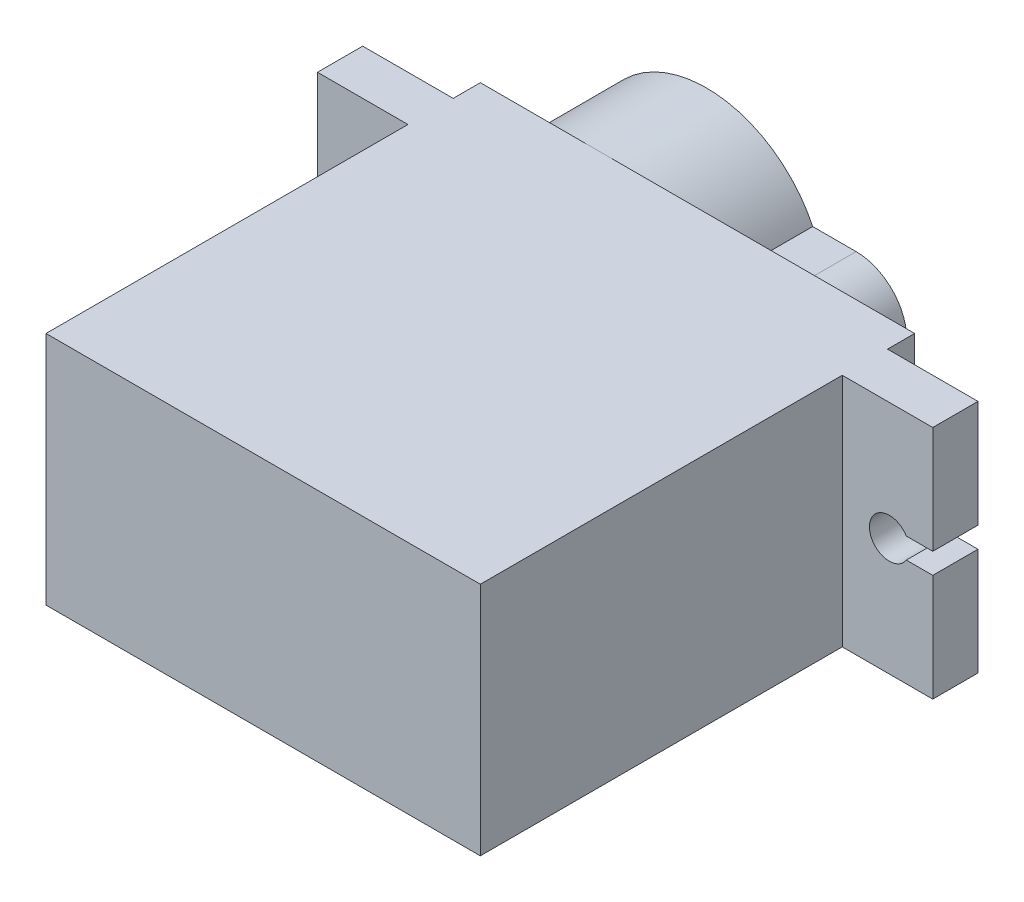
SolidWorks part; units mm, degrees
ref_plane "前视基准面" through (0, 0, 0) normal (0, 0, 1) x (1, 0, 0)
ref_plane "上视基准面" through (0, 0, 0) normal (0, 1, 0) x (1, 0, 0)
ref_plane "右视基准面" through (0, 0, 0) normal (1, 0, 0) x (0, 0, -1)
sketch "草图1" plane through (0, 0, 0) normal (0, 0, 1) x (1, 0, 0)
  line L0 (0, 0) -> (24, 0)
  line L5 (0, 0) -> (0, 13)
  line L6 (24, 0) -> (24, 13)
  line L7 (0, 13) -> (24, 13)
extrude "凸台-拉伸1" add sketch "草图1" along normal blind 24
ref_plane "基准面4" through (0, 0, 1.5) normal (0, 0, 1) x (1, 0, 0)
sketch "草图2" plane through (0, 0, 1.5) normal (0, 0, 1) x (1, 0, 0)
  line L0 (-5, 13) -> (29, 13)
  line L1 (-5, 13) -> (-5, 0)
  line L2 (29, 13) -> (29, 0)
  line L3 (-5, 0) -> (29, 0)
extrude "凸台-拉伸2" add sketch "草图2" along normal blind 2.5
ref_point "点2"
ref_point "点6"
ref_point "点7"
ref_point "点3"
sketch "草图6" plane through (0, 0, 1.5) normal (0, 0, 1) x (1, 0, 0)
  line L0 (-2.6, 6.5) -> (-2.6, 10)
  line L1 (-2.6, 6.5) -> (-2.6, 3)
  line L2 (-5, 7.0748) -> (-3.5379, 7.0748)
  line L3 (-5, 7.0748) -> (-5, 5.9252)
  line L4 (-5, 5.9252) -> (-3.5379, 5.9252)
  line L5 (12, 13) -> (12, 0) construction
  line L6 (29, 5.9252) -> (27.5379, 5.9252)
  line L7 (29, 7.0748) -> (29, 5.9252)
  line L8 (29, 7.0748) -> (27.5379, 7.0748)
  line L9 (26.6, 6.5) -> (26.6, 3)
  line L10 (26.6, 6.5) -> (26.6, 10)
  arc A0 (-3.5379, 5.9252) -> (-3.5379, 7.0748) centre (-2.6, 6.5) ccw
  arc A1 (27.5379, 5.9252) -> (27.5379, 7.0748) centre (26.6, 6.5) cw
ref_point "点4"
ref_point "点5"
hole_wizard "大小mm 暗销孔13" positions "草图24" profile "草图25" hole size "Ø1.0" standard "ISO"
sketch "草图24" plane through (0, 0, 1.5) normal (0, 0, -1) x (-1, 0, 0)
  point P0 (2.6, 10)
  point P3 (2.6, 3)
  point P6 (-26.6, 10)
  point P9 (-26.6, 3)
sketch "草图25" plane through (-2.6, 10, 1.5) normal (1, 0, 0) x (0, 1, 0)
  line L0 (0, 0) -> (0, 2)
  line L1 (0, 2) -> (1.1, 1.077)
  line L2 (1.1, 1.077) -> (1.1, 0)
  line L5 (1.1, 0) -> (0, 0)
  line L10 (0, 2) -> (-1.1, 1.077) construction
  line L11 (0, -6.35) -> (0, 107.95) construction
  dimension "孔直径" = 2.2
  dimension "孔深度" = 2
  dimension "导头角度" = 100
extrude "切除-拉伸1" cut sketch "草图6" along normal blind 3.5 contours A1 L8 L7 L6 | A0 L2 L3 L4
ref_point "点8"
ref_point "点9"
sketch "草图27" plane through (0, 0, 0) normal (0, 0, -1) x (-1, 0, 0)
  line L1 (0, 13) -> (0, 0) construction
  line L2 (0, 0) -> (-24, 0) construction
  line L3 (-14.7658, 3.7) -> (-12.366, 3.7)
  line L5 (-12.366, 9.3) -> (-14.7658, 9.3)
  arc A0 (-12.366, 3.7) -> (-12.366, 9.3) centre (-6.5, 6.5) ccw
  arc A2 (-14.7658, 9.3) -> (-14.7658, 3.7) centre (-14.7658, 6.5) ccw
extrude "凸台-拉伸3" add sketch "草图27" along normal blind 6
ref_point "点10"
sketch "草图42" plane through (0, 0, -6) normal (0, 0, -1) x (-1, 0, 0)
  circle A0 centre (-6.5, 6.5) radius 1
extrude "切除-拉伸2" cut sketch "草图42" against normal blind 4
